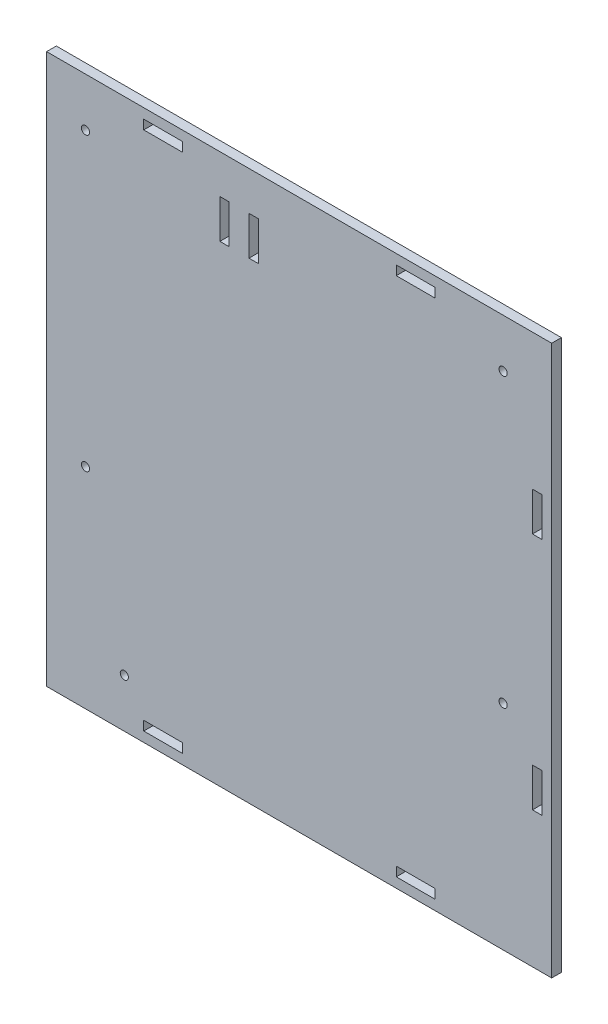
SolidWorks part; units mm, degrees
ref_plane "Front Plane" through (0, 0, 0) normal (0, 0, 1) x (1, 0, 0)
ref_plane "Top Plane" through (0, 0, 0) normal (0, 1, 0) x (1, 0, 0)
ref_plane "Right Plane" through (0, 0, 0) normal (1, 0, 0) x (0, 0, -1)
sketch "Sketch1" plane through (0, 0, 0) normal (0, 0, 1) x (1, 0, 0)
  line L0 (5, 278) -> (5, 208) construction
  line L1 (-250, -5) -> (10, -5)
  line L2 (-250, -5) -> (-250, 278)
  line L3 (-250, 278) -> (10, 278)
  line L4 (10, -5) -> (10, 278)
  line L5 (5, 278) -> (0, 278) construction
  line L6 (-200, 0) -> (-200, 5) construction
  line L7 (-200, 4.9) -> (-180, 4.9)
  line L8 (-200, 4.9) -> (-200, 0.1)
  line L9 (-200, 0.1) -> (-180, 0.1)
  line L10 (-180, 4.9) -> (-180, 0.1)
  line L11 (-180, 0) -> (-180, 5) construction
  line L12 (-70, 0) -> (-70, 5) construction
  line L13 (-70, 4.9) -> (-50, 4.9)
  line L14 (-70, 4.9) -> (-70, 0.1)
  line L15 (-70, 0.1) -> (-50, 0.1)
  line L16 (-50, 4.9) -> (-50, 0.1)
  line L17 (-50, 0) -> (-50, 5) construction
  line L18 (0, 85) -> (5, 85) construction
  line L19 (0.1, 85) -> (4.9, 85)
  line L20 (0.1, 85) -> (0.1, 65)
  line L21 (0.1, 65) -> (4.9, 65)
  line L22 (4.9, 85) -> (4.9, 65)
  line L23 (0, 65) -> (5, 65) construction
  line L24 (0, 65) -> (0, 85) construction
  line L25 (0, 208) -> (5, 208) construction
  line L26 (0.1, 208) -> (4.9, 208)
  line L27 (0.1, 208) -> (0.1, 188)
  line L28 (0.1, 188) -> (4.9, 188)
  line L29 (4.9, 208) -> (4.9, 188)
  line L30 (0, 208) -> (5, 208) construction
  line L31 (0, 188) -> (5, 188) construction
  line L32 (0, 188) -> (0, 208) construction
  line L33 (-70, 273) -> (-70, 268) construction
  line L34 (-70, 272.9) -> (-50, 272.9)
  line L35 (-70, 272.9) -> (-70, 268.1)
  line L36 (-70, 268.1) -> (-50, 268.1)
  line L37 (-50, 272.9) -> (-50, 268.1)
  line L38 (-50, 273) -> (-50, 268) construction
  line L39 (-70, 268) -> (-50, 268) construction
  line L40 (-200, 273) -> (-200, 268) construction
  line L41 (-200, 272.9) -> (-180, 272.9)
  line L42 (-200, 272.9) -> (-200, 268.1)
  line L43 (-200, 268.1) -> (-180, 268.1)
  line L44 (-180, 272.9) -> (-180, 268.1)
  line L45 (-180, 273) -> (-180, 268) construction
  line L46 (-200, 268) -> (-180, 268) construction
  line L47 (5, -5) -> (0, -5) construction
  line L48 (-250, 5) -> (-250, 0) construction
  dimension "D1" = 5
  dimension "D2" = 4.8
  dimension "D3" = 5.1
  dimension "D4" = 4.8
  dimension "D5" = 5.1
  dimension "D6" = 4.8
  dimension "D7" = 0.1
  dimension "D8" = 4.8
  dimension "D9" = 0.1
  dimension "D10" = 4.8
  dimension "D11" = 0.1
  dimension "D12" = 4.8
  dimension "D13" = 0.1
extrude "Boss-Extrude1" add sketch "Sketch1" along normal blind 5
sketch "Sketch2" plane through (0, 0, 5) normal (0, 0, 1) x (1, 0, 0)
  line L0 (-145.9052, 258) -> (-140.9052, 258) construction
  line L1 (-145.8052, 258) -> (-141.0052, 258)
  line L2 (-145.8052, 258) -> (-145.8052, 238)
  line L3 (-145.8052, 238) -> (-141.0052, 238)
  line L4 (-141.0052, 258) -> (-141.0052, 238)
  line L5 (-145.9052, 238) -> (-140.9052, 238) construction
  line L6 (-145.9052, 238) -> (-145.9052, 258) construction
  line L8 (-156.0052, 238) -> (-160.8052, 238)
  line L9 (-156.0052, 238) -> (-156.0052, 258)
  line L10 (-156.0052, 258) -> (-160.8052, 258)
  line L11 (-160.8052, 238) -> (-160.8052, 258)
  dimension "D1" = 4.8
  dimension "D2" = 0.1
  dimension "D3" = 4.8
  dimension "D4" = 15
extrude "Cut-Extrude1" cut sketch "Sketch2" against normal blind 5
sketch "Sketch3" plane through (0, 0, 5) normal (0, 0, 1) x (1, 0, 0)
  line L0 (10, 278) -> (-250, 278) construction
  line L1 (-250, 278) -> (-250, -5) construction
  line L2 (10, -5) -> (10, 278) construction
  circle A0 centre (-230, 253) radius 2.1
  circle A1 centre (-15, 253) radius 2.1
  dimension "D1" = 4.2
  dimension "D2" = 4.2
  dimension "D3" = 25
  dimension "D4" = 20
  dimension "D5" = 25
  dimension "D6" = 25
extrude "Cut-Extrude2" cut sketch "Sketch3" against normal blind 5
sketch "Sketch4" plane through (0, 0, 5) normal (0, 0, 1) x (1, 0, 0)
  line L0 (-250, -5) -> (10, -5) construction
  line L1 (-250, 278) -> (-250, -5) construction
  circle A0 centre (-210, 20) radius 2.1
  dimension "D1" = 25
  dimension "D2" = 40
  dimension "D3" = 4.2
extrude "Cut-Extrude3" cut sketch "Sketch4" against normal blind 5
sketch "Sketch5" plane through (0, 0, 5) normal (0, 0, 1) x (1, 0, 0)
  line L0 (10, -5) -> (10, 278) construction
  line L1 (-250, -5) -> (10, -5) construction
  circle A0 centre (-15, 105) radius 2.1
  dimension "D1" = 4.2
  dimension "D2" = 25
  dimension "D3" = 110
extrude "Cut-Extrude4" cut sketch "Sketch5" against normal blind 5
sketch "Sketch6" plane through (0, 0, 5) normal (0, 0, 1) x (1, 0, 0)
  circle A0 centre (-230, 103) radius 2.1
  dimension "D1" = 4.2
extrude "Cut-Extrude5" cut sketch "Sketch6" against normal blind 5
